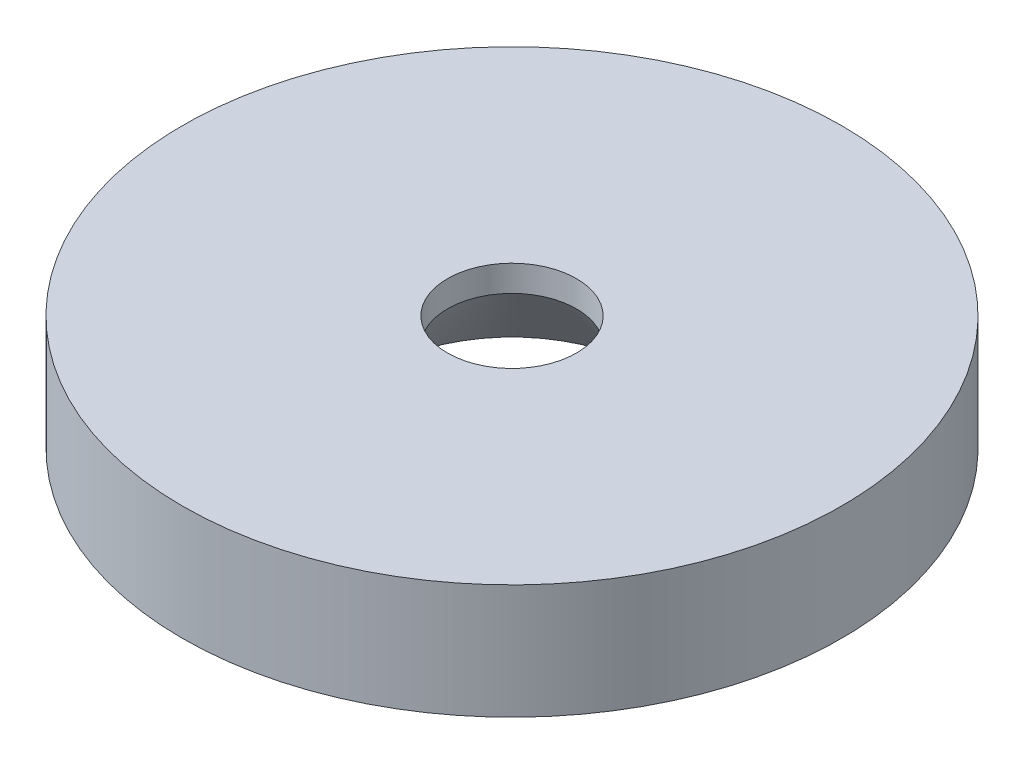
SolidWorks part; units mm, degrees
ref_plane "Front Plane" through (0, 0, 0) normal (0, 0, 1) x (1, 0, 0)
ref_plane "Top Plane" through (0, 0, 0) normal (0, 1, 0) x (1, 0, 0)
ref_plane "Right Plane" through (0, 0, 0) normal (1, 0, 0) x (0, 0, -1)
sketch "Sketch1" plane through (0, 0, 0) normal (0, 1, 0) x (1, 0, 0)
  circle A0 centre (0, 0) radius 11.5
  dimension "D1" = 23
extrude "Boss-Extrude1" add sketch "Sketch1" along normal blind 4
sketch "Sketch2" plane through (0, 4, 0) normal (0, 1, 0) x (1, 0, 0)
  circle A0 centre (0, 0) radius 2.25
  dimension "D1" = 4.5
extrude "Cut-Extrude1" cut sketch "Sketch2" against normal through all
chamfer "Chamfer1" distance 2.5 angle 51 1 edges at (0, 0, 2.25)
